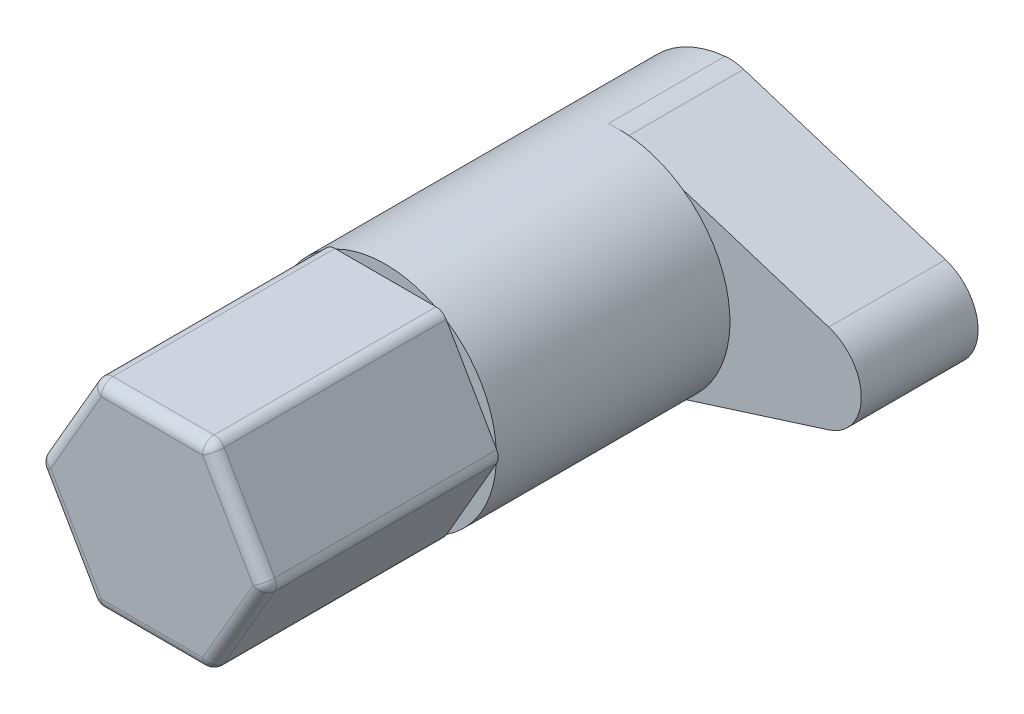
SolidWorks part; units mm, degrees
ref_plane "Front Plane" through (0, 0, 0) normal (0, 0, 1) x (1, 0, 0)
ref_plane "Top Plane" through (0, 0, 0) normal (0, 1, 0) x (1, 0, 0)
ref_plane "Right Plane" through (0, 0, 0) normal (1, 0, 0) x (0, 0, -1)
sketch "Sketch1" plane through (0, 0, 0) normal (0, 0, 1) x (1, 0, 0)
  line L1 (2.4537, -4.25) -> (4.9075, 0)
  line L2 (4.9075, 0) -> (2.4537, 4.25)
  line L3 (2.4537, 4.25) -> (-2.4537, 4.25)
  line L4 (-2.4537, 4.25) -> (-4.9075, 0)
  line L5 (-4.9075, 0) -> (-2.4537, -4.25)
  line L6 (-2.4537, -4.25) -> (2.4537, -4.25)
  circle A0 centre (0, 0) radius 4.25 construction
  dimension "D1" = 8.5
extrude "Boss-Extrude1" add sketch "Sketch1" along normal blind 10
fillet "Fillet1" radius 0.5 12 edges at (-3.6806, -2.125, 10) (-3.6806, 2.125, 10) (0, 4.25, 10) (3.6806, 2.125, 10) (3.6806, -2.125, 10) (0, -4.25, 10) (-2.4537, -4.25, 5) (-4.9075, 0, 5) (2.4537, -4.25, 5) (4.9075, 0, 5) (2.4537, 4.25, 5) (-2.4537, 4.25, 5)
sketch "Sketch2" plane through (0, 0, 0) normal (0, 0, -1) x (-1, 0, 0)
  circle A0 centre (0, 0) radius 4.75
  dimension "D1" = 9.5
extrude "Boss-Extrude2" add sketch "Sketch2" along normal blind 10
sketch "Sketch3" plane through (0, 0, -10) normal (0, 0, -1) x (-1, 0, 0)
  line L0 (0, 4.75) -> (-15, 0)
  line L1 (-15, 0) -> (0, -4.75)
  line L2 (-15, 0) -> (0, 0) construction
  arc A0 (0, -4.75) -> (0, 4.75) centre (0, 0) ccw
  arc A1 (0, 4.75) -> (-2.7342, 3.8842) centre (0, 0) ccw construction
  arc A2 (-2.7342, 3.8842) -> (-4.75, 0) centre (0, 0) ccw construction
  arc A3 (-4.75, 0) -> (-2.7342, -3.8842) centre (0, 0) ccw construction
  arc A4 (-2.7342, -3.8842) -> (0, -4.75) centre (0, 0) ccw construction
  circle A5 centre (0, 0) radius 4.75 construction
  dimension "D1" = 15
extrude "Boss-Extrude3" add sketch "Sketch3" along normal blind 5
fillet "Fillet2" radius 2 3 edges at (0, 4.75, -12.5) (0, -4.75, -12.5) (15, 0, -12.5)
